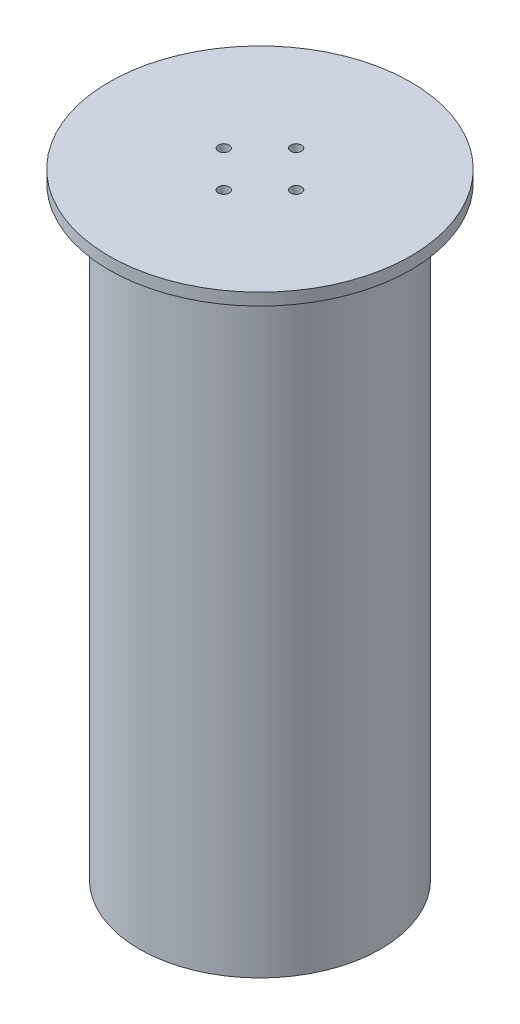
SolidWorks part; units mm, degrees
ref_plane "Plano frontal" through (0, 0, 0) normal (0, 0, 1) x (1, 0, 0)
ref_plane "Plano superior" through (0, 0, 0) normal (0, 1, 0) x (1, 0, 0)
ref_plane "Plano direito" through (0, 0, 0) normal (1, 0, 0) x (0, 0, -1)
sketch "Esboço1" plane through (0, 0, 0) normal (0, 0, 1) x (1, 0, 0)
  line L0 (0, 0) -> (0, 510) construction
  line L1 (0, 0) -> (400.3596, 0) construction
  line L2 (0, 510) -> (125, 510)
  line L3 (125, 510) -> (125, 500)
  line L4 (125, 500) -> (100, 500)
  line L5 (100, 500) -> (100, 0)
  line L6 (88, 0) -> (100, 0)
  line L7 (94, 10) -> (94, 500)
  line L8 (94, 500) -> (0, 500)
  line L9 (0, 510) -> (0, 500)
  line L10 (94, 10) -> (88, 10)
  line L11 (88, 10) -> (88, 0)
  dimension "D1" = 200
  dimension "D2" = 6
  dimension "D3" = 10
  dimension "D4" = 250
  dimension "D5" = 500
  dimension "D6" = 10
  dimension "D7" = 6
revolve "Revolução1" add sketch "Esboço1" angle 360 about L0
sketch "Esboço2" plane through (0, 510, 0) normal (0, 1, 0) x (1, 0, 0)
  circle A0 centre (0, 30) radius 4.5
  circle A1 centre (0, 0) radius 30 construction
  circle A2 centre (30, 0) radius 4.5
  circle A3 centre (0, -30) radius 4.5
  circle A4 centre (-30, 0) radius 4.5
  point P14 (0, 0)
  dimension "D1" = 60
  dimension "D2" = 9
  dimension "D3" = 4
extrude "Corte-extrusão1" cut sketch "Esboço2" against normal up to next
